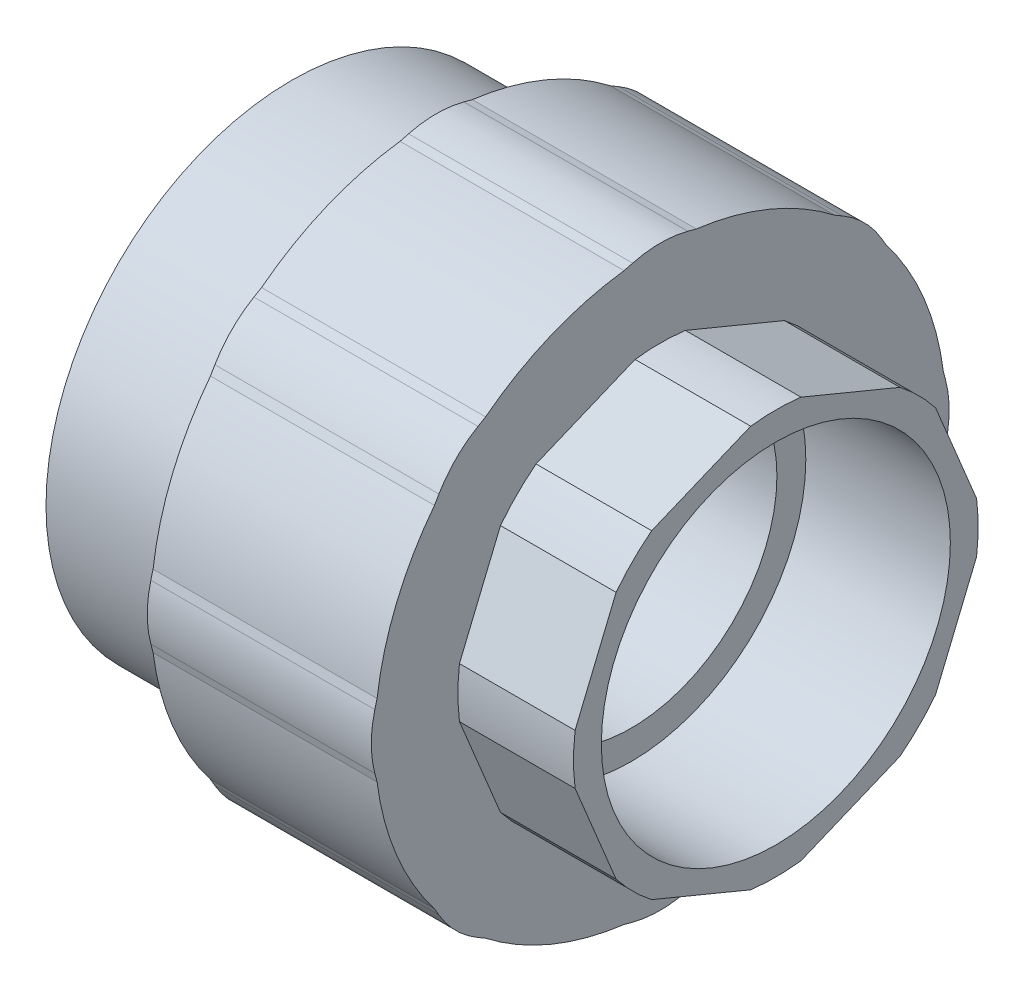
SolidWorks part; units mm, degrees
ref_plane "Front Plane" through (0, 0, 0) normal (0, 0, 1) x (1, 0, 0)
ref_plane "Top Plane" through (0, 0, 0) normal (0, 1, 0) x (1, 0, 0)
ref_plane "Right Plane" through (0, 0, 0) normal (1, 0, 0) x (0, 0, -1)
sketch "Sketch1" plane through (0, 0, 0) normal (0, 0, 1) x (1, 0, 0)
  line L0 (0, -25) -> (23.5, -25)
  line L1 (23.5, -25) -> (23.5, -20.15)
  line L2 (23.5, -20.15) -> (47, -20.15)
  line L3 (47, -20.15) -> (47, -24.15)
  line L4 (47, -24.15) -> (67, -24.15)
  line L5 (67, -24.15) -> (67, -28)
  line L8 (20, -34) -> (0, -34)
  line L9 (0, -34) -> (0, -25)
  line L10 (0, 0) -> (67, 0) construction
  line L11 (20, -39.5) -> (51, -39.5)
  line L12 (51, -39.5) -> (51, -28)
  line L13 (51, -28) -> (67, -28)
  line L14 (20, -34) -> (20, -39.5)
  dimension "D1" = 67
  dimension "D2" = 24.15
  dimension "D3" = 28
  dimension "D4" = 20
  dimension "D5" = 23.5
  dimension "D6" = 16
  dimension "D7" = 9
  dimension "D8" = 39.5
  dimension "D9" = 20.15
  dimension "D10" = 25
  dimension "D11" = 20
revolve "Revolve1" add sketch "Sketch1" angle 360 about L10
sketch "Sketch3" plane through (67, 0, 0) normal (1, 0, 0) x (0, 0, -1)
  line L7 (0, 29.2246) -> (-20.6649, 20.6649)
  line L8 (-20.6649, 20.6649) -> (-29.2246, 0)
  line L9 (-29.2246, 0) -> (-20.6649, -20.6649)
  line L10 (-20.6649, -20.6649) -> (0, -29.2246)
  line L11 (0, -29.2246) -> (20.6649, -20.6649)
  line L12 (20.6649, -20.6649) -> (29.2246, 0)
  line L13 (29.2246, 0) -> (20.6649, 20.6649)
  line L14 (20.6649, 20.6649) -> (0, 29.2246)
  circle A0 centre (0, 0) radius 27 construction
  circle A1 centre (0, 0) radius 45.8839
  dimension "D1" = 54
extrude "Cut-Extrude1" cut sketch "Sketch3" against normal up to surface (16 mm away) up to face at (51, 0, 28)
sketch "Sketch4" plane through (51, 0, 0) normal (1, 0, 0) x (0, 0, -1)
  line L0 (0, 39.5) -> (0, 40.5) construction
  line L1 (-3.8227, 39.4925) -> (-5, 39.1823)
  line L2 (3.8227, 39.4925) -> (5, 39.1823)
  line L3 (-5, 39.1823) -> (5, 39.1823)
  circle A0 centre (0, 0) radius 39.5 construction
  arc A1 (3.8227, 39.4925) -> (-3.8227, 39.4925) centre (0, 24.9878) ccw
  dimension "D3" = 15
  dimension "D1" = 10
  dimension "D2" = 1
extrude "Boss-Extrude1" add sketch "Sketch4" against normal up to surface (31 mm away) up to face at (20, 0, 39.5)
pattern_circular "CirPattern1" count 8 over 360 about axis through (0, 0, 0) along (1, 0, 0) of "Boss-Extrude1"
